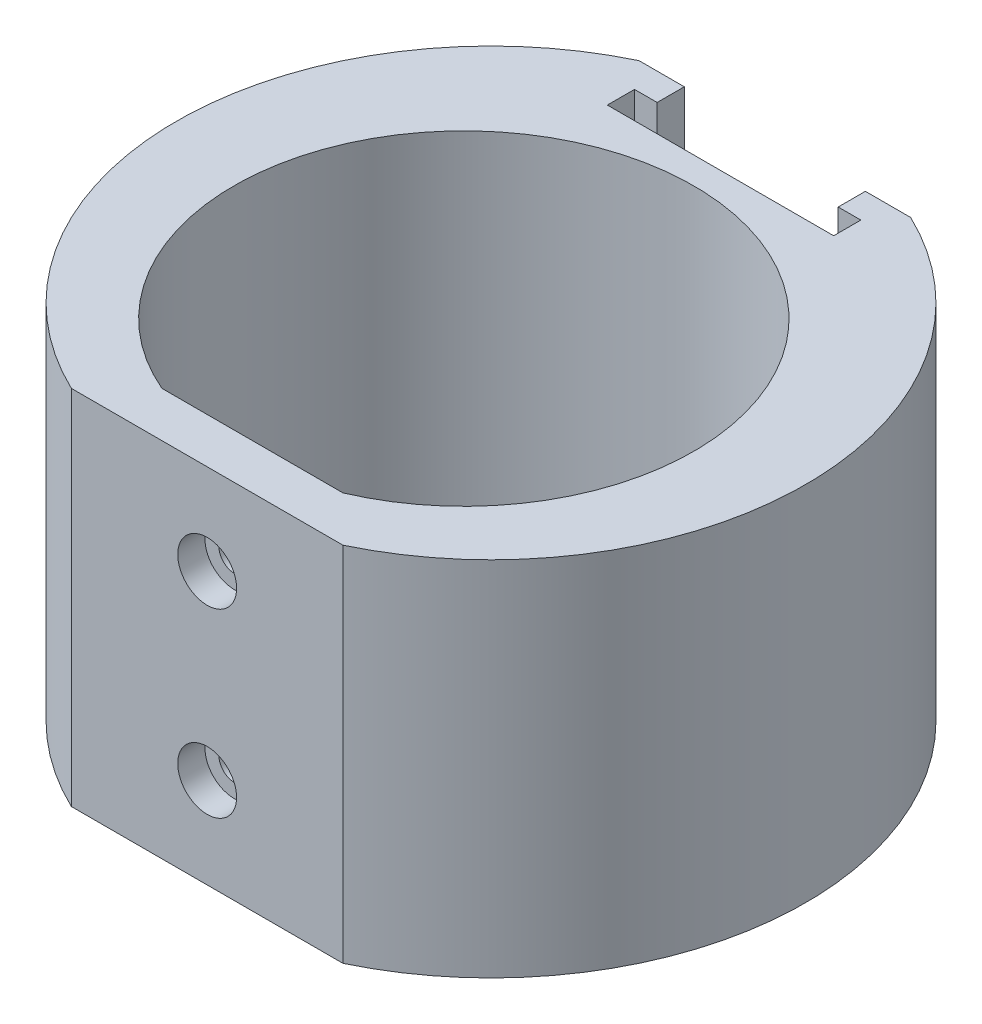
SolidWorks part; units mm, degrees
ref_plane "Front Plane" through (0, 0, 0) normal (0, 0, 1) x (1, 0, 0)
ref_plane "Top Plane" through (0, 0, 0) normal (0, 1, 0) x (1, 0, 0)
ref_plane "Right Plane" through (0, 0, 0) normal (1, 0, 0) x (0, 0, -1)
sketch "Sketch1" plane through (0, 0, 0) normal (0, 1, 0) x (1, 0, 0)
  line L0 (-10, -23.3487) -> (10, -23.3487)
  line L1 (-15, -28.3487) -> (15, -28.3487)
  line L2 (-15, 34.3487) -> (15, 34.3487)
  arc A0 (10, -23.3487) -> (-10, -23.3487) centre (0, 0) ccw
  arc A1 (15, -28.3487) -> (15, 34.3487) centre (0, 3) ccw
  arc A2 (-15, 34.3487) -> (-15, -28.3487) centre (0, 3) ccw
  dimension "D1" = 25.4
  dimension "D4" = 30
  dimension "D2" = 20
  dimension "D3" = 3
  dimension "D5" = 5
  dimension "D6" = 30
extrude "Boss-Extrude1" add sketch "Sketch1" along normal mid plane 40
ref_plane "Plane1" through (0, 0, -37.7525) normal (0, 0, -1) x (-1, 0, 0)
sketch "Sketch2" plane through (0, 0, -37.7525) normal (0, 0, -1) x (-1, 0, 0)
  line L1 (-10, -7.5) -> (10, -7.5)
  line L2 (-10, -7.5) -> (-10, 7.5)
  line L3 (-10, 7.5) -> (10, 7.5)
  line L4 (10, -7.5) -> (10, 7.5)
  line L5 (-10, -7.5) -> (10, 7.5) construction
  line L6 (-10, 7.5) -> (10, -7.5) construction
  point P0 (0, 0)
  dimension "D1" = 20
  dimension "D2" = 15
sketch "Sketch3" plane through (0, 20, 0) normal (0, 1, 0) x (1, 0, 0)
  line L0 (-10, 34.3487) -> (-10, 31.3487)
  line L2 (10, 31.3487) -> (10, 34.3487)
  line L3 (-10, 34.3487) -> (10, 34.3487)
  line L4 (15, 34.3487) -> (-15, 34.3487) construction
  line L5 (-10, 31.3487) -> (-12.5, 31.3487)
  line L6 (-12.5, 31.3487) -> (-12.5, 28.3487)
  line L7 (-12.5, 28.3487) -> (12.5, 28.3487)
  line L8 (12.5, 28.3487) -> (12.5, 31.3487)
  line L9 (12.5, 31.3487) -> (10, 31.3487)
  point P4 (0, 34.3487)
  point P5 (0, 34.3487)
  point P12 (0, 28.3487)
  dimension "D1" = 20
  dimension "D2" = 3
  dimension "D3" = 3
  dimension "D4" = 25
extrude "Cut-Extrude1" cut sketch "Sketch3" against normal up to vertex (27.5 mm away) up to point (10, -7.5, -37.7525)
hole_wizard "CBORE for M3 SHCS1" positions "Sketch5" profile "Sketch6" counterbore size "M3" standard "ANSI Metric" end condition up to next
sketch "Sketch5" plane through (0, 0, 28.3487) normal (0, 0, 1) x (1, 0, 0)
  line L0 (0, 10) -> (0, -10) construction
  line L2 (-15, 20) -> (15, 20) construction
  point P0 (0, 10)
  point P2 (0, -10)
  point P12 (0, 0)
  dimension "D1" = 10
sketch "Sketch6" plane through (0, 10, 28.3487) normal (1, 0, 0) x (0, -1, 0)
  line L0 (0, 0) -> (0, 5)
  line L1 (0, 5) -> (1.7, 5)
  line L3 (1.7, 5) -> (1.7, 3)
  line L4 (1.7, 3) -> (3.25, 3)
  line L5 (3.25, 3) -> (3.25, 0)
  line L7 (3.25, 0) -> (0, 0)
  line L11 (0, -6.35) -> (0, 107.95) construction
  dimension "Thru Hole Dia." = 3.4
  dimension "Thru Hole Depth" = 5
  dimension "C'Bore Dia." = 6.5
  dimension "C'Bore Depth" = 3
fillet "Fillet1" radius 2 4 edges at (10, -7.5, -32.8487) (-10, -7.5, -32.8487) (-12.5, -7.5, -29.8487) (12.5, -7.5, -29.8487)
